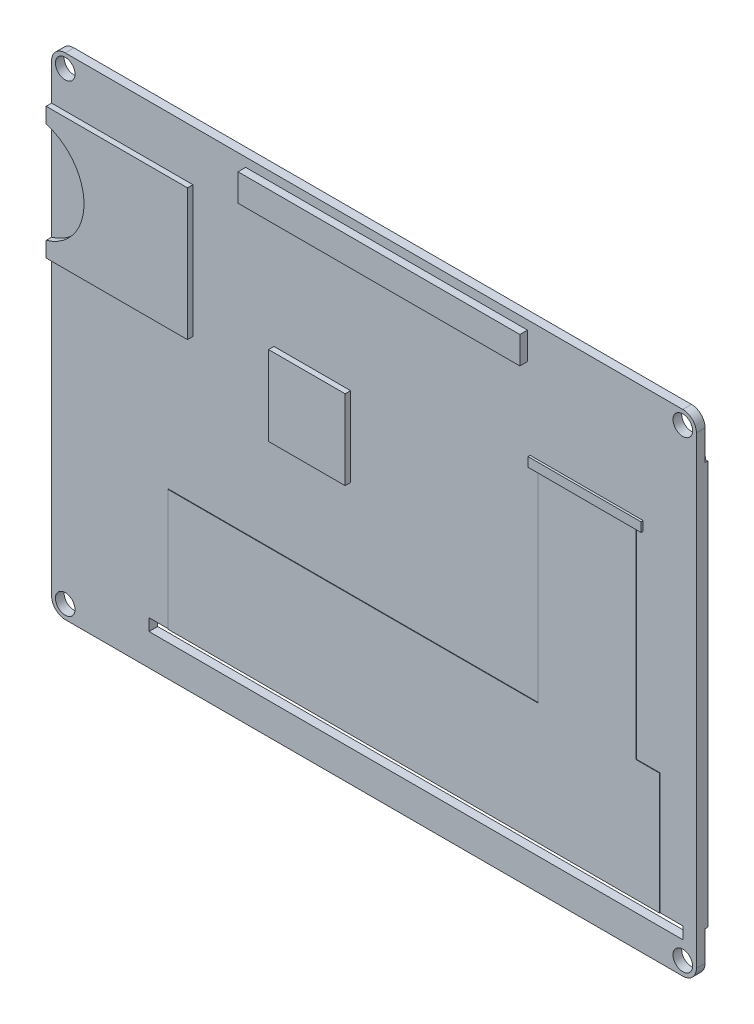
SolidWorks part; units mm, degrees
ref_plane "Front Plane" through (0, 0, 0) normal (0, 0, 1) x (1, 0, 0)
ref_plane "Top Plane" through (0, 0, 0) normal (0, 1, 0) x (1, 0, 0)
ref_plane "Right Plane" through (0, 0, 0) normal (1, 0, 0) x (0, 0, -1)
sketch "Sketch1" plane through (0, 0, 0) normal (0, 0, 1) x (1, 0, 0)
  line L0 (-41.35, -39.3) -> (56.75, -39.3)
  line L1 (-56.75, 45.1) -> (56.75, 45.1)
  line L2 (-59.25, 42.6) -> (-59.25, -42.6)
  line L3 (-56.75, -45.1) -> (56.75, -45.1)
  line L4 (59.25, 42.6) -> (59.25, -42.6)
  line L5 (-59.25, 45.1) -> (59.25, -45.1) construction
  line L6 (-59.25, -45.1) -> (59.25, 45.1) construction
  line L8 (56.75, -39.3) -> (56.75, -37.1)
  line L9 (56.75, -37.1) -> (-41.35, -37.1)
  line L10 (-41.35, -37.1) -> (-41.35, -39.3)
  arc A0 (-56.75, -45.1) -> (-59.25, -42.6) centre (-56.75, -42.6) cw
  arc A1 (56.75, -45.1) -> (59.25, -42.6) centre (56.75, -42.6) ccw
  arc A2 (59.25, 42.6) -> (56.75, 45.1) centre (56.75, 42.6) ccw
  arc A3 (-56.75, 45.1) -> (-59.25, 42.6) centre (-56.75, 42.6) ccw
  circle A4 centre (-56.75, 42.6) radius 1.8
  circle A5 centre (-56.75, -42.6) radius 1.8
  circle A6 centre (56.75, -42.6) radius 1.8
  circle A7 centre (56.75, 42.6) radius 1.8
  point P0 (0, 0)
  dimension "D3" = 2.5
  dimension "D4" = 2.5
  dimension "D5" = 3.6
  dimension "D6" = 3.6
  dimension "D7" = 3.6
  dimension "D8" = 3.6
  dimension "D1" = 90.2
  dimension "D2" = 118.5
  dimension "D9" = 2.2
extrude "Boss-Extrude1" add sketch "Sketch1" along normal blind 1.6
ref_plane "Plane1" through (0, 0, 1.6) normal (0, 0, 1) x (1, 0, 0)
sketch "Sketch2" plane through (0, 0, 1.6) normal (0, 0, 1) x (1, 0, 0)
  line L0 (-59.25, 42.6) -> (-59.25, -42.6) construction
  line L1 (-59.25, 35.8529) -> (-33.2802, 35.8529)
  line L2 (-59.25, 35.8529) -> (-59.25, 11.6906)
  line L3 (-59.25, 11.6906) -> (-33.2802, 11.6906)
  line L4 (-33.2802, 35.8529) -> (-33.2802, 11.6906)
  line L5 (-59.25, 35.8529) -> (-59.25, 32.999)
  line L6 (-59.25, 11.6906) -> (-59.25, 14.5731)
  arc A0 (-59.25, 14.5182) -> (-59.25, 33.0253) centre (-61.9312, 23.7718) ccw
extrude "Boss-Extrude2" add sketch "Sketch2" along normal blind 1 contours A0 L6 L3 L4 L1 L2
sketch "Sketch4" plane through (0, 0, 1.6) normal (0, 0, 1) x (1, 0, 0)
  line L1 (-18.383, 17.5629) -> (-4.3053, 17.5629)
  line L2 (-18.383, 17.5629) -> (-18.383, 2.9385)
  line L3 (-18.383, 2.9385) -> (-4.3053, 2.9385)
  line L4 (-4.3053, 17.5629) -> (-4.3053, 2.9385)
extrude "Boss-Extrude3" add sketch "Sketch4" along normal blind 1
sketch "Sketch5" plane through (0, 0, 0) normal (0, 0, 1) x (1, 0, 0)
  line L1 (28.702, 23.7718) -> (49.4768, 23.7718)
  line L2 (28.702, 23.7718) -> (28.702, 22.0732)
  line L3 (28.702, 22.0732) -> (49.4768, 22.0732)
  line L4 (49.4768, 23.7718) -> (49.4768, 22.0732)
extrude "Boss-Extrude4" add sketch "Sketch5" along normal blind 2
sketch "Sketch6" plane through (0, 0, 1.6) normal (0, 0, 1) x (1, 0, 0)
  line L0 (56.75, -37.1) -> (-41.35, -37.1) construction
  line L1 (30.2275, 21.9782) -> (48.2275, 21.9782)
  line L2 (30.2275, 21.9782) -> (30.2275, -14.8316)
  line L3 (30.2275, -14.8316) -> (-37.7781, -14.8316)
  line L4 (48.2275, 21.9782) -> (48.2275, -14.8316)
  line L5 (52.5454, -14.8316) -> (48.2275, -14.8316)
  line L6 (52.5454, -14.8316) -> (52.5454, -37.1)
  line L7 (52.5454, -37.1) -> (-37.7781, -37.1)
  line L8 (-37.7781, -14.8316) -> (-37.7781, -37.1)
  dimension "D1" = 18
extrude "Boss-Extrude5" add sketch "Sketch6" along normal blind 0.1
sketch "Sketch7" plane through (0, 0, 0) normal (0, 0, 1) x (1, 0, 0)
  line L0 (59.25, -42.6) -> (59.25, 42.6) construction
  line L1 (-59.25, 37.1) -> (59.25, 37.1)
  line L2 (-59.25, 37.1) -> (-59.25, -37.1)
  line L3 (-59.25, -37.1) -> (59.25, -37.1)
  line L4 (59.25, 37.1) -> (59.25, -37.1)
  line L5 (-59.25, 37.1) -> (59.25, -37.1) construction
  line L6 (-59.25, -37.1) -> (59.25, 37.1) construction
  point P0 (0, 0)
extrude "Boss-Extrude6" add sketch "Sketch7" against normal blind 2.5
ref_plane "Plane2" through (0, 0, -2.5) normal (0, 0, -1) x (-1, 0, 0)
sketch "Sketch9" plane through (0, 0, -2.5) normal (0, 0, -1) x (-1, 0, 0)
  line L1 (59.25, -37.1) -> (-59.25, -37.1)
  line L2 (59.25, -37.1) -> (59.25, 37.1)
  line L3 (59.25, 37.1) -> (-59.25, 37.1)
  line L4 (-59.25, -37.1) -> (-59.25, 37.1)
  line L5 (59.25, -37.1) -> (-59.25, 37.1) construction
  line L6 (59.25, 37.1) -> (-59.25, -37.1) construction
  line L7 (56.785, -35.5565) -> (-56.785, -35.5565)
  line L8 (56.785, -35.5565) -> (56.785, 35.5565)
  line L9 (56.785, 35.5565) -> (-56.785, 35.5565)
  line L10 (-56.785, -35.5565) -> (-56.785, 35.5565)
  line L11 (56.785, -35.5565) -> (-56.785, 35.5565) construction
  line L12 (56.785, 35.5565) -> (-56.785, -35.5565) construction
  point P0 (0, 0)
  point P7 (0, 0)
extrude "Cut-Extrude1" cut sketch "Sketch9" against normal blind 2
sketch "Sketch10" plane through (0, 0, 0) normal (0, 0, 1) x (1, 0, 0)
  line L1 (28.2062, 38.4499) -> (-23.5952, 38.4499)
  line L2 (28.2062, 38.4499) -> (28.2062, 43.4559)
  line L3 (28.2062, 43.4559) -> (-23.5952, 43.4559)
  line L4 (-23.5952, 38.4499) -> (-23.5952, 43.4559)
  line L5 (28.2062, 38.4499) -> (-23.5952, 43.4559) construction
  line L6 (28.2062, 43.4559) -> (-23.5952, 38.4499) construction
  point P0 (2.3055, 40.9529)
extrude "Boss-Extrude7" add sketch "Sketch10" along normal blind 3
